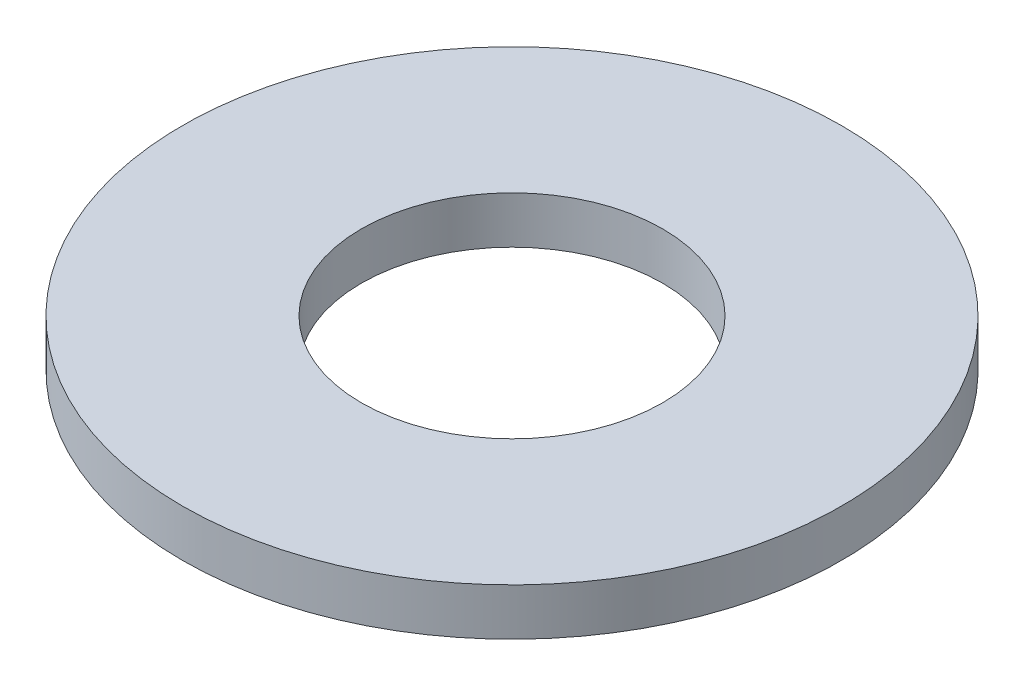
SolidWorks part; units mm, degrees
material "AISI 304"
ref_plane "前视基准面" through (0, 0, 0) normal (0, 0, 1) x (1, 0, 0)
ref_plane "上视基准面" through (0, 0, 0) normal (0, 1, 0) x (1, 0, 0)
ref_plane "右视基准面" through (0, 0, 0) normal (1, 0, 0) x (0, 0, -1)
sketch "草图1" plane through (0, 0, 0) normal (0, 1, 0) x (1, 0, 0)
  circle A0 centre (0, 0) radius 1.6
  circle A1 centre (0, 0) radius 3.5
  dimension "D1" = 3.2
  dimension "D2" = 7
extrude "凸台-拉伸1" add sketch "草图1" along normal blind 0.5
